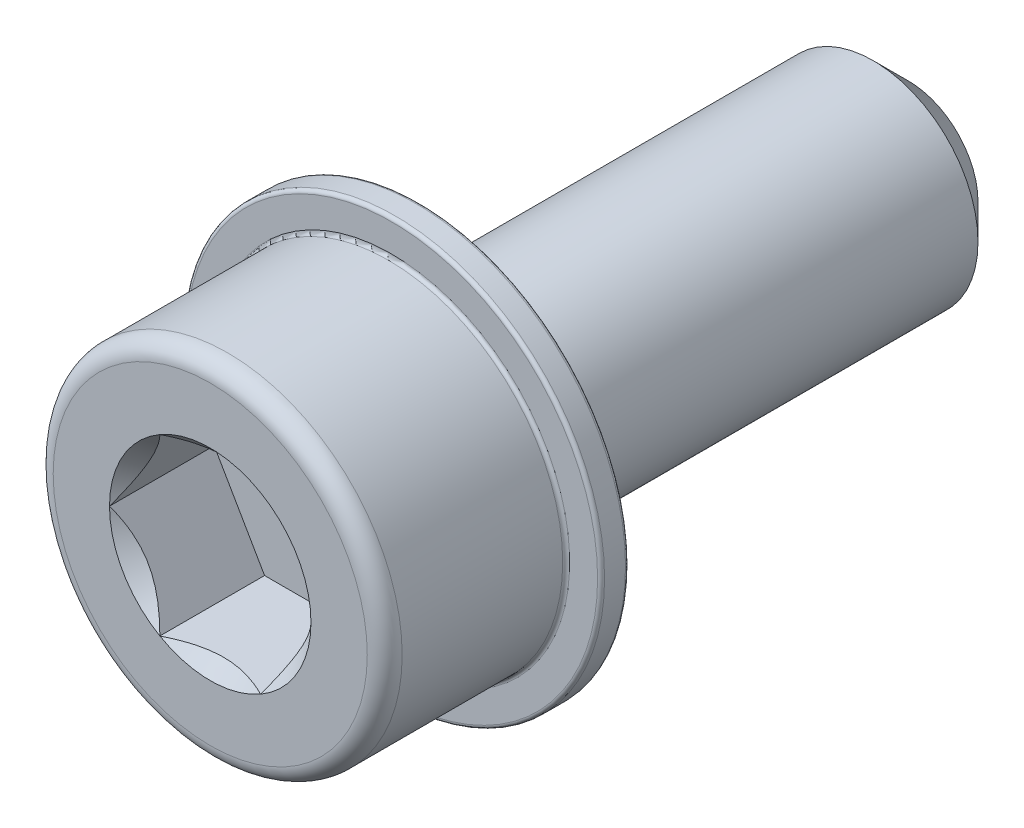
SolidWorks part; units mm, degrees
material "Acciaio inossidabile (ferroso)"
ref_plane "Piano frontale" through (0, 0, 0) normal (0, 0, 1) x (1, 0, 0)
ref_plane "Piano superiore" through (0, 0, 0) normal (0, 1, 0) x (1, 0, 0)
ref_plane "Piano destro" through (0, 0, 0) normal (1, 0, 0) x (0, 0, -1)
sketch "Schizzo1" plane through (0, 0, 0) normal (0, 0, 1) x (1, 0, 0)
  circle A0 centre (0, 0) radius 3
  dimension "D1" = 6
extrude "Estrusione-Estrusione1" add sketch "Schizzo1" along normal blind 14
cosmetic thread "Filettatura cosmetica2" parameters "D2"=4.891
chamfer "Smusso1" distance 1 angle 45 1 edges at (3, 0, 0)
sketch "Schizzo6" plane through (0, 0, 14) normal (0, 0, 1) x (1, 0, 0)
  circle A0 centre (0, 0) radius 5
  dimension "D1" = 10
extrude "Estrusione-Estrusione3" add sketch "Schizzo6" along normal blind 6
sketch "Schizzo7" plane through (0, 0, 20) normal (0, 0, 1) x (1, 0, 0)
  line L1 (1.4434, 2.5) -> (-1.4434, 2.5)
  line L2 (-1.4434, 2.5) -> (-2.8868, 0)
  line L3 (-2.8868, 0) -> (-1.4434, -2.5)
  line L4 (-1.4434, -2.5) -> (1.4434, -2.5)
  line L5 (1.4434, -2.5) -> (2.8868, 0)
  line L6 (2.8868, 0) -> (1.4434, 2.5)
  circle A1 centre (0, 0) radius 2.5 construction
  dimension "D1" = 5
extrude "Taglio-Estrusione3" cut sketch "Schizzo7" against normal blind 3
sketch "Schizzo8" plane through (0, 0, 20) normal (0, 0, 1) x (1, 0, 0)
  circle A0 centre (0, 0) radius 2.8868
extrude "Taglio-Estrusione4" cut sketch "Schizzo8" against normal blind 1 draft 45
fillet "Raccordo1" radius 0.5 1 edges at (5, 0, 20)
sketch "Schizzo9" plane through (0, 0, 14) normal (0, 0, -1) x (-1, 0, 0)
  circle A0 centre (0, 0) radius 5
  circle A1 centre (0, 0) radius 6
  dimension "D1" = 10
  dimension "D2" = 12
extrude "Estrusione-Estrusione4" add sketch "Schizzo9" against normal blind 0.8
fillet "Raccordo3" radius 0.1 3 edges at (-5, 0, 14.8) (-6, 0, 14.8) (-6, 0, 14)
